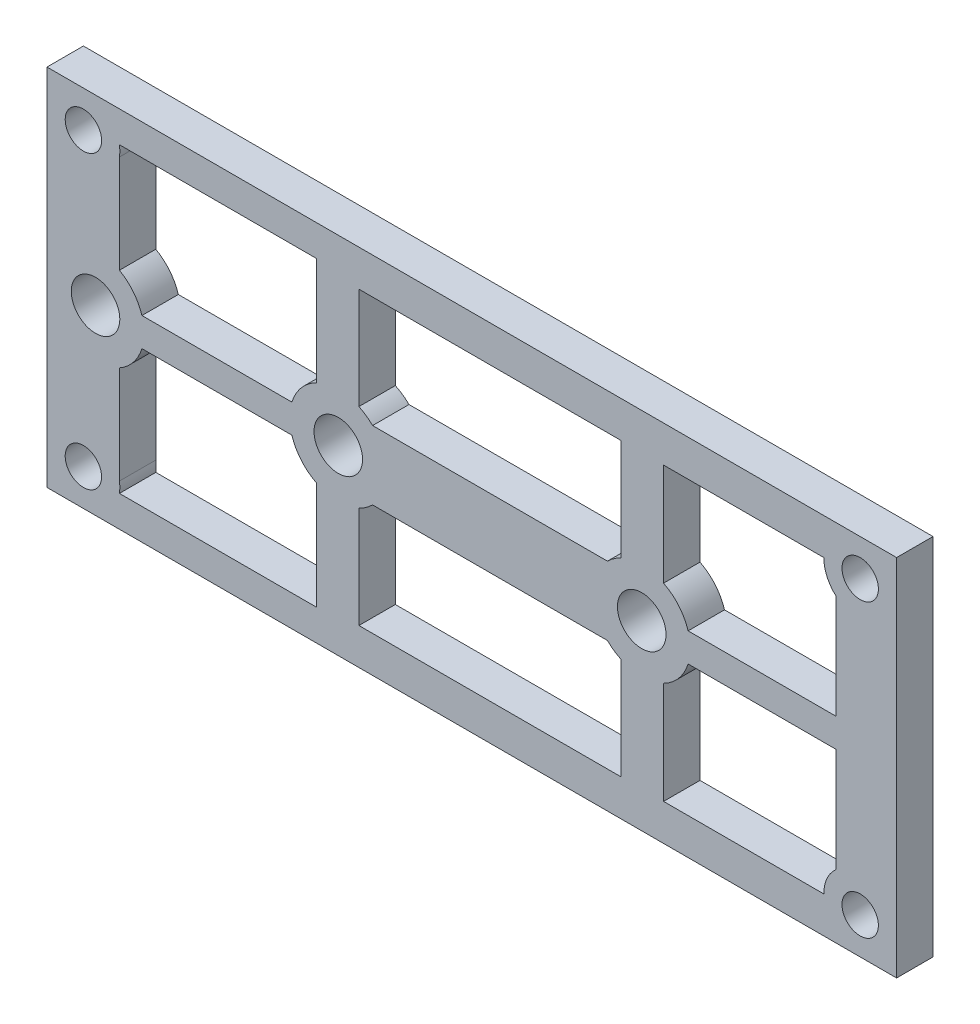
SolidWorks part; units mm, degrees
ref_plane "Front Plane" through (0, 0, 0) normal (0, 0, 1) x (1, 0, 0)
ref_plane "Top Plane" through (0, 0, 0) normal (0, 1, 0) x (1, 0, 0)
ref_plane "Right Plane" through (0, 0, 0) normal (1, 0, 0) x (0, 0, -1)
sketch "Sketch1" plane through (0, 0, 0) normal (0, 0, 1) x (1, 0, 0)
  line L1 (35, -15) -> (-35, -15)
  line L2 (35, -15) -> (35, 15)
  line L3 (35, 15) -> (-35, 15)
  line L4 (-35, -15) -> (-35, 15)
  line L5 (35, -15) -> (-35, 15) construction
  line L6 (35, 15) -> (-35, -15) construction
  point P0 (0, 0)
  dimension "D1" = 70
  dimension "D2" = 30
extrude "Boss-Extrude1" add sketch "Sketch1" along normal blind 3
sketch "Sketch2" plane through (0, 0, 3) normal (0, 0, 1) x (1, 0, 0)
  line L0 (-35, 15) -> (-35, -15) construction
  line L2 (35, 15) -> (-35, 15) construction
  line L3 (-29.0325, 12.4402) -> (-12.8, 12.4402)
  line L4 (35, -15) -> (35, 15) construction
  line L5 (-29.0325, 11.5598) -> (-29.0325, 3.4826)
  line L6 (0, -1.65) -> (0, 1.65) construction
  line L7 (1.65, 0) -> (-1.65, 0) construction
  line L8 (-27.178, 1.18) -> (-14.822, 1.18)
  line L9 (-12.8, 12.4402) -> (-12.8, 3.5721)
  line L10 (11.1745, 2.8313) -> (-8.1745, 2.8313)
  line L11 (12.3, 3.6208) -> (12.3, 12)
  line L12 (12.3, 12) -> (-9.3, 12)
  line L13 (-9.3, 3.6208) -> (-9.3, 12)
  line L14 (30, 1.18) -> (17.822, 1.18)
  line L15 (30, 1.18) -> (30, 9.7639)
  line L16 (29, 12) -> (15.8, 12)
  line L17 (15.8, 3.5721) -> (15.8, 12)
  circle A0 centre (32, 12) radius 1.5
  circle A1 centre (-32, 12) radius 1.5
  circle A2 centre (32, -12) radius 1.5
  circle A3 centre (-32, -12) radius 1.5
  circle A4 centre (-11, 0) radius 2
  circle A5 centre (-31, 0) radius 2
  circle A6 centre (14, 0) radius 2
  arc A7 (-8.1745, 2.8313) -> (-9.3, 3.6208) centre (-11, 0) ccw
  arc A8 (12.3, 3.6208) -> (11.1745, 2.8313) centre (14, 0) ccw
  arc A9 (-27.178, 1.18) -> (-29.0325, 3.4826) centre (-31, 0) ccw
  arc A10 (-29.0325, 11.5598) -> (-29.0325, 12.4402) centre (-32, 12) ccw
  arc A17 (29, 12) -> (30, 9.7639) centre (32, 12) ccw
  arc A18 (-12.8, 3.5721) -> (-14.822, 1.18) centre (-11, 0) ccw
  arc A19 (17.822, 1.18) -> (15.8, 3.5721) centre (14, 0) ccw
  point P28 (-29.0204, 13.0128)
  point P29 (0, 0)
  point P42 (11.1745, 2.8313)
  dimension "D1" = 3
  dimension "D4" = 4
  dimension "D5" = 4
  dimension "D8" = 8
  dimension "D9" = 8
  dimension "D10" = 8
  dimension "D11" = 4
  dimension "D12" = 4
  dimension "D13" = 6
  dimension "D14" = 6
  dimension "D15" = 16.2325
  dimension "D16" = 8.0771
  dimension "D2" = 3
  dimension "D3" = 3
  dimension "D6" = 20
  dimension "D7" = 25
  dimension "D17" = 3.5
  dimension "D18" = 3.5
  dimension "D19" = 12.356
  dimension "D20" = 2
  dimension "D21" = 1.7
  dimension "D22" = 1.8
extrude "Cut-Extrude2" cut sketch "Sketch2" against normal through all
mirror "Mirror1" about plane through (0, 0, 0) normal (0, 1, 0) of "Cut-Extrude2"
